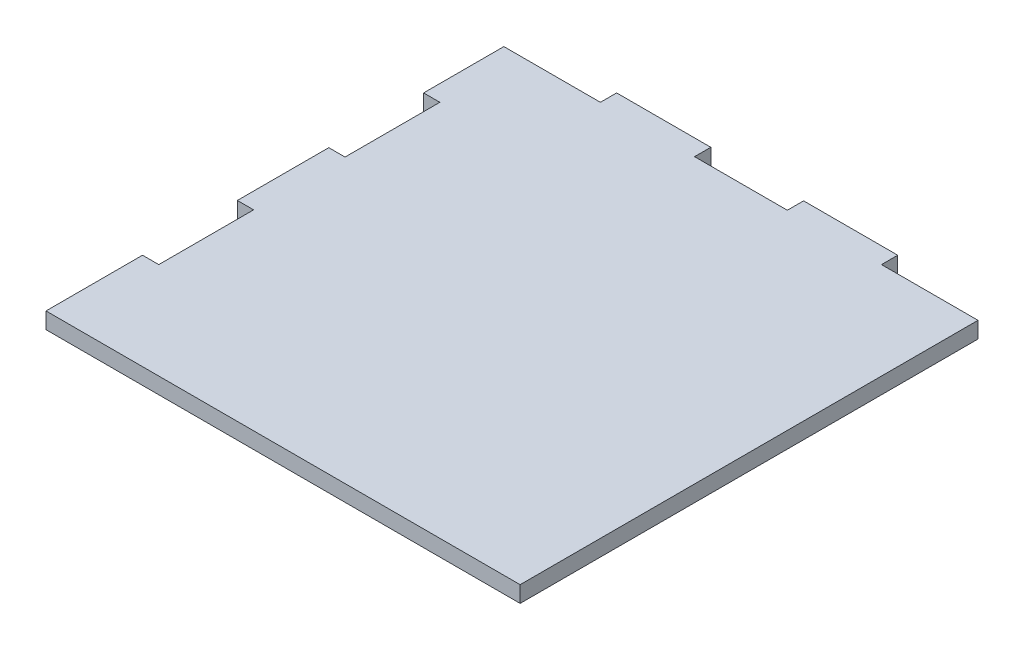
SolidWorks part; units mm, degrees
material "Maple"
ref_plane "Front Plane" through (0, 0, 0) normal (0, 0, 1) x (1, 0, 0)
ref_plane "Top Plane" through (0, 0, 0) normal (0, 1, 0) x (1, 0, 0)
ref_plane "Right Plane" through (0, 0, 0) normal (1, 0, 0) x (0, 0, -1)
sketch "Sketch1" plane through (0, 0, 0) normal (0, 1, 0) x (1, 0, 0)
  line L0 (209.25, 350) -> (278.75, 350)
  line L1 (0, 0) -> (350, 0)
  line L2 (0, 0) -> (0, 71.25)
  line L3 (71.25, 350) -> (140.75, 350)
  line L7 (0, 338) -> (71.25, 338)
  line L8 (71.25, 350) -> (71.25, 338)
  line L11 (350, 338) -> (278.75, 338)
  line L12 (278.75, 350) -> (278.75, 338)
  line L14 (140.75, 350) -> (140.75, 338)
  line L15 (140.75, 338) -> (209.25, 338)
  line L16 (209.25, 350) -> (209.25, 338)
  line L17 (0, 278.75) -> (0, 338)
  line L18 (0, 278.75) -> (12, 278.75)
  line L20 (0, 208.75) -> (12, 208.75)
  line L21 (12, 278.75) -> (12, 208.75)
  line L22 (0, 141.25) -> (12, 141.25)
  line L24 (0, 71.25) -> (12, 71.25)
  line L25 (12, 141.25) -> (12, 71.25)
  line L26 (0, 141.25) -> (0, 208.75)
  line L27 (350, 338) -> (350, 0)
  dimension "D2" = 350
  dimension "D3" = 69.5
  dimension "D4" = 70
  dimension "D6" = 12
  dimension "D7" = 69.5
  dimension "D8" = 71.25
  dimension "D9" = 70
  dimension "D11" = 71.25
  dimension "D12" = 12
  dimension "D13" = 350
extrude "Boss-Extrude1" add sketch "Sketch1" along normal blind 12
